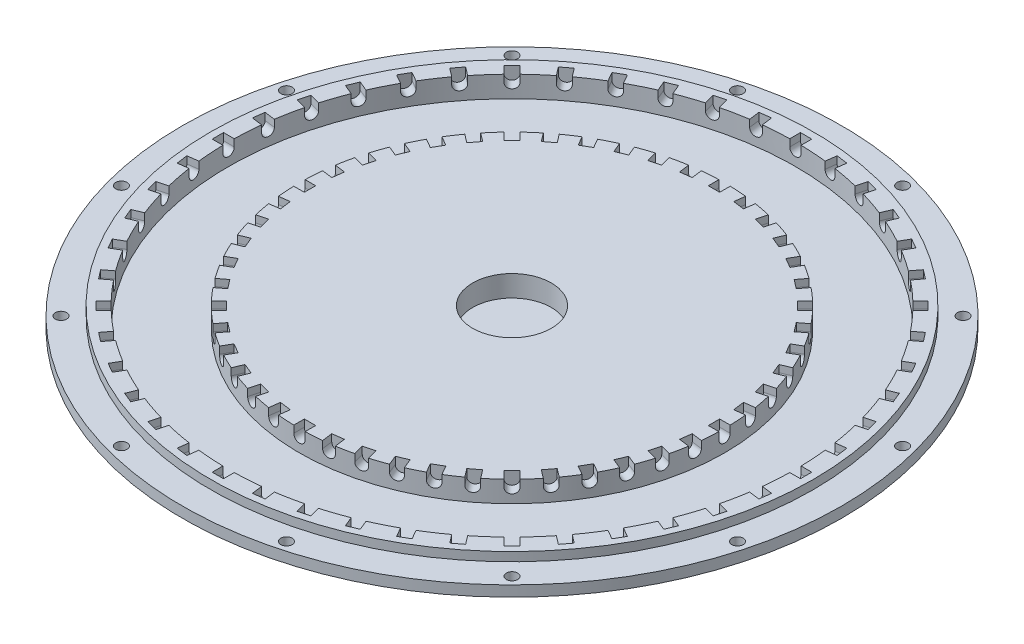
SolidWorks part; units mm, degrees
ref_plane "Front Plane" through (0, 0, 0) normal (0, 0, 1) x (1, 0, 0)
ref_plane "Top Plane" through (0, 0, 0) normal (0, 1, 0) x (1, 0, 0)
ref_plane "Right Plane" through (0, 0, 0) normal (1, 0, 0) x (0, 0, -1)
ref_axis "RevolutionAxis" through (0, 8.925, 0) along (0, -1, 0)
sketch "Esquisse1" plane through (0, 0, 0) normal (0, 0, 1) x (1, 0, 0)
  line L0 (-93, 3.5) -> (-83, 3.5)
  line L1 (-83, 3.5) -> (-83, 0)
  line L2 (-93, 3.5) -> (-93, 6.5)
  line L3 (-93, 6.5) -> (-85, 6.5)
  line L4 (-85, 6.5) -> (-85, 9)
  line L5 (-83, 0) -> (-55, 0)
  line L6 (-55, 0) -> (-55, 6)
  line L7 (-55, 6) -> (-14.1, 6)
  line L8 (0, 0) -> (0, 3)
  line L9 (0, 3) -> (-11.1, 3)
  line L10 (-11.1, 3) -> (-11.1, 9)
  line L11 (-11.1, 9) -> (-60, 9)
  line L12 (-60, 9) -> (-60, 3)
  line L13 (-60, 3) -> (-80, 3)
  line L14 (-80, 3) -> (-80, 9)
  line L15 (-80, 9) -> (-85, 9)
  line L16 (-14.1, 6) -> (-14.1, 0)
  line L17 (-14.1, 0) -> (0, 0)
  dimension "D1" = 11.1
  dimension "D2" = 6
  dimension "D4" = 6
  dimension "D5" = 60
  dimension "D6" = 80
  dimension "D7" = 3
  dimension "D8" = 5
  dimension "D9" = 8
  dimension "D10" = 2.5
  dimension "D11" = 93
  dimension "D12" = 85
  dimension "D13" = 5
  dimension "D14" = 3
  dimension "D15" = 3
  dimension "D16" = 3
  dimension "D17" = 3
  dimension "D18" = 20
revolve "MainRevolution" add sketch "Esquisse1" angle 360 about L8
ref_plane "MiddleCylinderPlan" through (70, 0, 0) normal (1, 0, 0) x (0, 0, -1)
sketch "Esquisse3" plane through (70, 0, 0) normal (1, 0, 0) x (0, 0, -1)
  line L0 (-1.6, 9) -> (1.6, 9)
  line L1 (1.6, 9) -> (1.6, 7)
  line L2 (-1.6, 9) -> (-1.6, 7)
  line L3 (0, 4.95) -> (0, -4.95) construction
  line L4 (11.1, 9) -> (-11.1, 9) construction
  arc A0 (1.6, 7) -> (-1.6, 7) centre (0, 7) cw
  point P4 (2.4344, 8.5)
  point P6 (-1.6, 6)
  point P7 (0, 0)
  dimension "D2" = 1.6
  dimension "D1" = 3.2
  dimension "D3" = 2
extrude "HolesToFixCylinder" cut sketch "Esquisse3" against normal mid plane 26
sketch "Esquisse4" plane through (0, 6.5, 0) normal (0, 1, 0) x (1, 0, 0)
  line L0 (0, 0) -> (86.9333, -23.2937) construction
  line L1 (0, 0) -> (99.7714, 0) construction
  circle A0 centre (86.9333, -23.2937) radius 1.6
  dimension "D1" = 3.2
  dimension "D2" = 90
  dimension "D3" = 15
extrude "HolesToFixMain" cut sketch "Esquisse4" against normal through all
pattern_circular "HolesToFixCylinderRepetition" count 48 over 360 about axis through (0, 0, 0) along (0, 1, 0) of "HolesToFixCylinder"
pattern_circular "HolesToFixMainRepetition" count 12 over 360 about axis through (0, 0, 0) along (0, 1, 0) of "HolesToFixMain"
sketch "Esquisse5" plane through (0, 0, 0) normal (0, 0, 1) x (1, 0, 0)
  line L1 (11.1, 0) -> (56, 0)
  line L2 (11.1, 0) -> (11.1, 6)
  line L3 (11.1, 6) -> (56, 6)
  line L4 (56, 0) -> (56, 6)
  line L6 (0, 8.925) -> (0, -0.425) construction
  line L8 (-83, 0) -> (83, 0) construction
  circle A0 centre (21.1, 3) radius 1.3
  circle A1 centre (31.1, 3) radius 1.3
  circle A2 centre (41.1, 3) radius 1.3
  point P10 (0, 0)
  point P14 (11, 0)
  point P16 (8.6827, 0)
  dimension "D1" = 2.6
  dimension "D2" = 10
  dimension "D3" = 3
  dimension "D4" = 10
  dimension "D5" = 10
  dimension "D6" = 11.1
  dimension "D7" = 6
  dimension "D8" = 56
extrude "Reinforcement" add sketch "Esquisse5" along normal mid plane 10
pattern_circular "ReinforcementRepetition" count 8 over 360 about axis through (0, 8.925, 0) along (0, -1, 0) of "Reinforcement"
